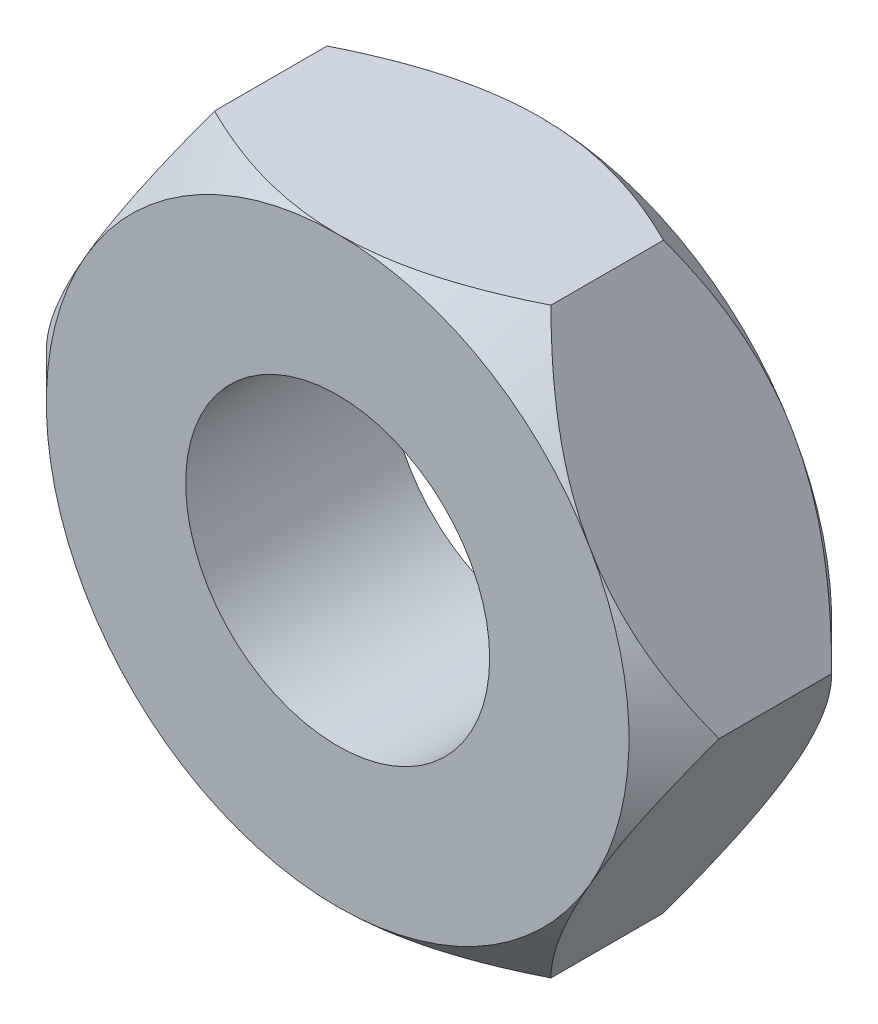
SolidWorks part; units mm, degrees
ref_plane "Front Plane" through (0, 0, 0) normal (0, 0, 1) x (1, 0, 0)
ref_plane "Top Plane" through (0, 0, 0) normal (0, 1, 0) x (1, 0, 0)
ref_plane "Right Plane" through (0, 0, 0) normal (1, 0, 0) x (0, 0, -1)
sketch "Sketch1" plane through (0, 0, 0) normal (0, 0, 1) x (1, 0, 0)
  line L1 (9.9593, 0) -> (4.9796, 8.625)
  line L2 (4.9796, 8.625) -> (-4.9796, 8.625)
  line L3 (-4.9796, 8.625) -> (-9.9593, 0)
  line L4 (-9.9593, 0) -> (-4.9796, -8.625)
  line L5 (-4.9796, -8.625) -> (4.9796, -8.625)
  line L6 (4.9796, -8.625) -> (9.9593, 0)
  circle A0 centre (0, 0) radius 8.625 construction
  circle A1 centre (0, 0) radius 4.5
  point P10 (-273.0954, -28.9066)
  dimension "D1" = 17.25
extrude "Boss-Extrude1" add sketch "Sketch1" along normal blind 6 contours L3 L4 L5 L6 L1 L2
sketch "Sketch2" plane through (0, 0, 6) normal (0, 0, 1) x (1, 0, 0)
  circle A0 centre (0, 0) radius 8.625
extrude "Cut-Extrude1" cut sketch "Sketch2" against normal blind 6 draft 45 flip side to cut
sketch "Sketch3" plane through (0, 0, 0) normal (0, 0, -1) x (-1, 0, 0)
  circle A0 centre (0, 0) radius 8.625
extrude "Cut-Extrude2" cut sketch "Sketch3" against normal blind 6 draft 45 flip side to cut
sketch "Sketch4" plane through (0, 0, 6) normal (0, 0, 1) x (1, 0, 0)
  circle A0 centre (0, 0) radius 4.5
extrude "Cut-Extrude3" cut sketch "Sketch4" against normal through all
